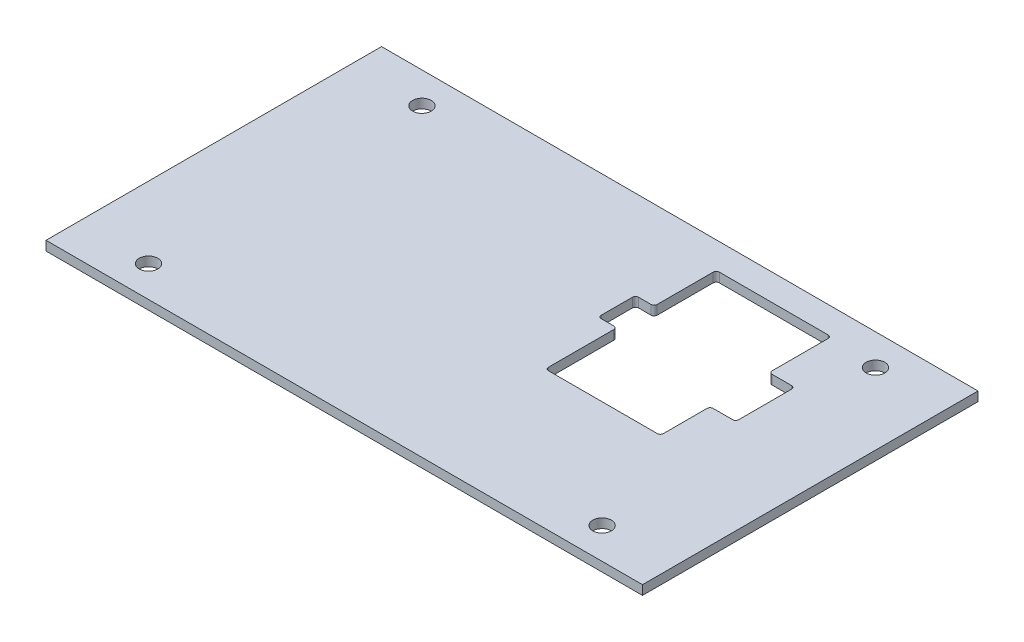
SolidWorks part; units mm, degrees
ref_plane "Спереди" through (0, 0, 0) normal (0, 0, 1) x (1, 0, 0)
ref_plane "Сверху" through (0, 0, 0) normal (0, 1, 0) x (1, 0, 0)
ref_plane "Справа" through (0, 0, 0) normal (1, 0, 0) x (0, 0, -1)
sketch "Эскиз1" plane through (0, 0, 0) normal (0, 1, 0) x (1, 0, 0)
  line L1 (-96, -54) -> (96, -54)
  line L2 (-96, -54) -> (-96, 54)
  line L3 (-96, 54) -> (96, 54)
  line L4 (96, -54) -> (96, 54)
  line L5 (-96, -54) -> (96, 54) construction
  line L6 (-96, 54) -> (96, -54) construction
  dimension "D1" = 192
  dimension "D2" = 108
extrude "Бобышка-Вытянуть1" add sketch "Эскиз1" along normal blind 3
sketch "Эскиз2" plane through (0, 3, 0) normal (0, 1, 0) x (1, 0, 0)
  line L0 (20.25, 45.5) -> (20.25, 25.5)
  line L1 (20.25, 25.5) -> (14.25, 25.5)
  line L2 (14.25, 25.5) -> (14.25, 13.5)
  line L3 (14.25, 13.5) -> (20.25, 13.5)
  line L4 (20.25, 13.5) -> (20.25, -9.5)
  line L5 (20.25, -9.5) -> (57.25, -9.5)
  line L6 (57.25, -9.5) -> (57.25, 6.5)
  line L7 (57.25, 6.5) -> (65.5, 6.5)
  line L8 (65.5, 6.5) -> (65.5, 25.5)
  line L9 (65.5, 25.5) -> (57.25, 25.5)
  line L10 (57.25, 25.5) -> (57.25, 45.5)
  line L11 (57.25, 45.5) -> (20.25, 45.5)
  line L12 (20.25, 45.5) -> (20.25, -9.5) construction
  circle A0 centre (-73, 44) radius 3
  circle A1 centre (73, 44) radius 3
  circle A2 centre (-73, -44) radius 3
  circle A3 centre (73, -44) radius 3
  point P20 (20.25, 18)
  point P25 (38.75, 18)
  point P29 (38.75, -9.5)
  dimension "D3" = 12
  dimension "D4" = 6
  dimension "D5" = 44
  dimension "D6" = 44
  dimension "D7" = 44
  dimension "D8" = 44
  dimension "D11" = 73
  dimension "D12" = 73
  dimension "D13" = 37
  dimension "D15" = 20
  dimension "D16" = 6
  dimension "D18" = 20
  dimension "D19" = 16
  dimension "D20" = 8.25
  dimension "D22" = 38.75
  dimension "D23" = 18
  dimension "D24" = 19
extrude "Вырез-Вытянуть1" cut sketch "Эскиз2" against normal through all
fillet "Скругление1" radius 1 12 edges at (57.25, 1.5, 9.5) (20.25, 1.5, 9.5) (20.25, 1.5, -13.5) (14.25, 1.5, -13.5) (65.5, 1.5, -25.5) (65.5, 1.5, -6.5) (57.25, 1.5, -6.5) (57.25, 1.5, -25.5) (20.25, 1.5, -25.5) (14.25, 1.5, -25.5) (57.25, 1.5, -45.5) (20.25, 1.5, -45.5)
